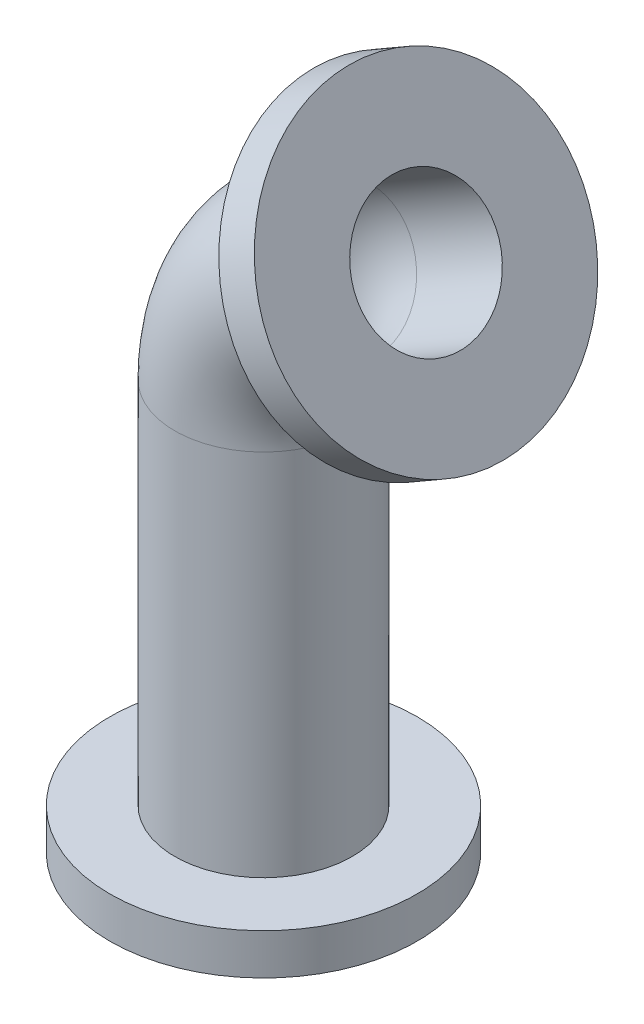
SolidWorks part; units mm, degrees
material "---"
ref_plane "Vorne" through (0, 0, 0) normal (0, 0, 1) x (1, 0, 0)
ref_plane "Oben" through (0, 0, 0) normal (0, 1, 0) x (1, 0, 0)
ref_plane "Rechts" through (0, 0, 0) normal (1, 0, 0) x (0, 0, -1)
sketch "Skizze1" plane through (0, 0, 0) normal (0, 0, 1) x (1, 0, 0)
  line L0 (0, 0) -> (0, 120)
  line L1 (22.5, 158.9711) -> (47.6147, 173.4711)
  arc A0 (22.5, 158.9711) -> (0, 120) centre (45, 120) ccw
  dimension "D2" = 45
  dimension "D1" = 120
  dimension "D3" = 120
  dimension "D4" = 29
sketch "Skizze2" plane through (0, 0, 0) normal (0, 1, 0) x (1, 0, 0)
  circle A0 centre (0, 0) radius 20
  dimension "D1" = 40
sweep "Austragung-Dünn1" add profiles "Skizze2" path "Skizze1" parameters "D1"=6
sketch "Skizze3" plane through (0, 0, 0) normal (0, -1, 0) x (1, 0, 0)
  circle A0 centre (0, 0) radius 45
  circle A1 centre (0, 0) radius 26 construction
  circle A2 centre (0, 0) radius 26
  dimension "D1" = 90
extrude "Aufsatz-Linear austragen1" add sketch "Skizze3" against normal blind 12
sketch "Skizze4" plane through (110.8263, 63.9856, 0) normal (0.866, 0.5, 0) x (0, 0, -1)
  circle A0 centre (0, 126.423) radius 20 construction
  circle A1 centre (0, 126.423) radius 20
  circle A2 centre (0, 126.423) radius 45
  dimension "D1" = 90
extrude "Aufsatz-Linear austragen2" add sketch "Skizze4" against normal blind 12
